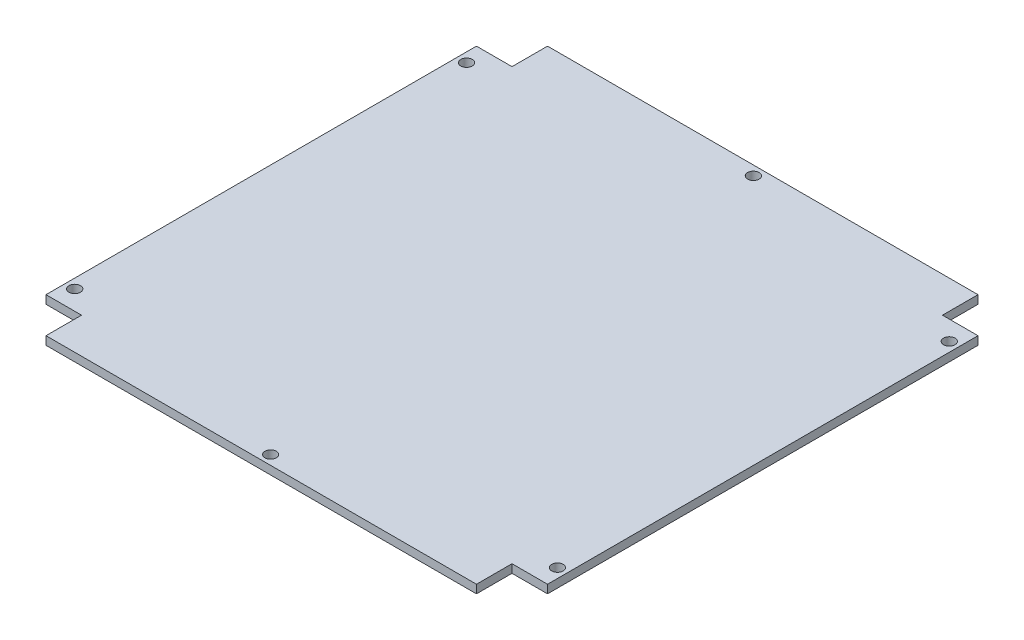
SolidWorks part; units mm, degrees
material "電力回路基板"
ref_plane "Front Plane" through (0, 0, 0) normal (0, 0, 1) x (1, 0, 0)
ref_plane "Top Plane" through (0, 0, 0) normal (0, 1, 0) x (1, 0, 0)
ref_plane "Right Plane" through (0, 0, 0) normal (1, 0, 0) x (0, 0, -1)
sketch "Sketch1" plane through (0, 0, 0) normal (0, 1, 0) x (1, 0, 0)
  line L0 (-34.1444, 27.6285) -> (-27.1444, 27.6285)
  line L1 (-27.1444, 34.6285) -> (55.2556, 34.6285)
  line L2 (55.2556, 34.6285) -> (55.2556, 27.6285)
  line L3 (55.2556, 27.6285) -> (62.2556, 27.6285)
  line L4 (62.2556, 27.6285) -> (62.2556, -54.7715)
  line L5 (62.2556, -54.7715) -> (55.2556, -54.7715)
  line L6 (55.2556, -54.7715) -> (55.2556, -61.7715)
  line L7 (55.2556, -61.7715) -> (-27.1444, -61.7715)
  line L8 (-27.1444, -61.7715) -> (-27.1444, -54.7715)
  line L9 (-27.1444, -54.7715) -> (-34.1444, -54.7715)
  line L10 (-34.1444, -54.7715) -> (-34.1444, 27.6285)
  line L11 (-27.1444, 27.6285) -> (-27.1444, 34.6285)
  dimension "D1" = 7
  dimension "D2" = 82.4
  dimension "D3" = 82.4
  dimension "D4" = 7
  dimension "D5" = 7
  dimension "D6" = 7
  dimension "D7" = 7
  dimension "D8" = 7
extrude "Boss-Extrude1" add sketch "Sketch1" along normal blind 1.6 contours L10 L0 L11 L1 L2 L3 L4 L5 L6 L7 L8 L9
hole_wizard "Ø2.2 (2.2) Diameter Hole1" positions "Sketch6" profile "Sketch5" hole size "Ø2.2" standard "ANSI Metric"
sketch "Sketch6" plane through (0, 1.6, 0) normal (0, 1, 0) x (1, 0, 0)
  line L7 (-34.1444, -54.7715) -> (-34.1444, 27.6285) construction
  line L8 (62.2556, 27.6285) -> (62.2556, -54.7715) construction
  line L9 (55.2556, -61.7715) -> (-27.1444, -61.7715) construction
  line L10 (-27.1444, 34.6285) -> (55.2556, 34.6285) construction
  line L13 (62.2556, 27.6285) -> (62.2556, -54.7715) construction
  line L14 (-34.1444, -54.7715) -> (-34.1444, 27.6285) construction
  line L15 (-34.1444, 27.6285) -> (-27.1444, 27.6285) construction
  line L16 (62.2556, -54.7715) -> (55.2556, -54.7715) construction
  line L17 (-27.1444, -54.7715) -> (-34.1444, -54.7715) construction
  line L18 (55.2556, 27.6285) -> (62.2556, 27.6285) construction
  point P4 (14.0556, 32.6285)
  point P6 (14.0556, -59.7715)
  point P8 (-32.1444, -51.0715)
  point P10 (60.2556, 23.9285)
  point P50 (-32.1444, 23.9285)
  point P52 (60.2556, -51.0715)
  dimension "D2" = 2
  dimension "D3" = 2
  dimension "D4" = 2
  dimension "D5" = 2
  dimension "D6" = 3.7
  dimension "D7" = 48.2
  dimension "D8" = 48.2
  dimension "D9" = 3.7
  dimension "D10" = 2
  dimension "D11" = 3.7
  dimension "D12" = 2
  dimension "D13" = 3.7
sketch "Sketch5" plane through (14.0556, 1.6, -32.6285) normal (1, 0, 0) x (0, 0, 1)
  line L0 (0, 0) -> (0, 5)
  line L1 (0, 5) -> (1.1, 5)
  line L2 (1.1, 5) -> (1.1, 0)
  line L5 (1.1, 0) -> (0, 0)
  line L10 (0, 5) -> (-1.1, 5) construction
  line L11 (0, -6.35) -> (0, 107.95) construction
  dimension "Hole Dia." = 2.2
  dimension "Hole Depth" = 5
  dimension "Drill Angle" = 180
sketch "Sketch8" plane through (0, 1.6, 0) normal (0, 1, 0) x (1, 0, 0)
  line L0 (55.2556, 34.6285) -> (55.2556, 27.6285) construction
  line L1 (-27.1444, 34.6285) -> (55.2556, 34.6285)
  line L2 (-27.1444, 34.6285) -> (-27.1444, 34.4285)
  line L3 (-27.1444, 34.4285) -> (55.2556, 34.4285)
  line L4 (55.2556, 34.6285) -> (55.2556, 34.4285)
  line L5 (62.2556, -54.7715) -> (55.2556, -54.7715) construction
  line L6 (62.2556, 27.6285) -> (62.0556, 27.6285)
  line L7 (62.2556, 27.6285) -> (62.2556, -54.7715)
  line L8 (62.2556, -54.7715) -> (62.0556, -54.7715)
  line L9 (62.0556, 27.6285) -> (62.0556, -54.7715)
  line L10 (-27.1444, -61.7715) -> (-27.1444, -54.7715) construction
  line L11 (55.2556, -61.7715) -> (-27.1444, -61.7715)
  line L12 (55.2556, -61.7715) -> (55.2556, -61.5715)
  line L13 (55.2556, -61.5715) -> (-27.1444, -61.5715)
  line L14 (-27.1444, -61.7715) -> (-27.1444, -61.5715)
  line L15 (-34.1444, 27.6285) -> (-27.1444, 27.6285) construction
  line L16 (-34.1444, -54.7715) -> (-33.9444, -54.7715)
  line L17 (-34.1444, -54.7715) -> (-34.1444, 27.6285)
  line L18 (-34.1444, 27.6285) -> (-33.9444, 27.6285)
  line L19 (-33.9444, -54.7715) -> (-33.9444, 27.6285)
  dimension "D1" = 0.2
  dimension "D2" = 0.2
  dimension "D3" = 0.2
  dimension "D4" = 0.2
extrude "Extrude1" cut sketch "Sketch8" against normal through all
